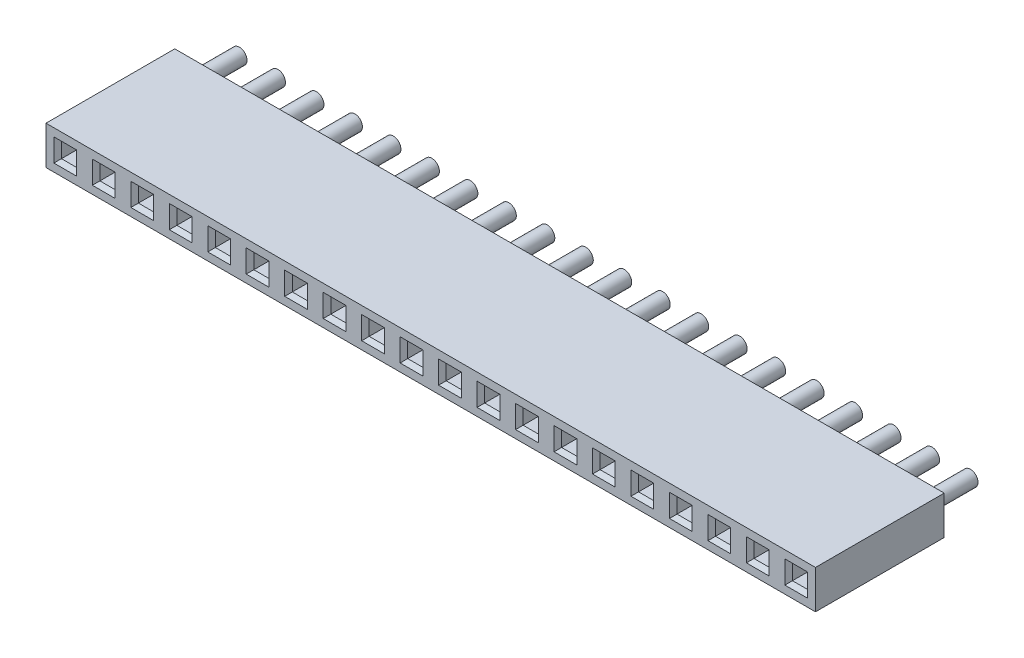
SolidWorks part; units mm, degrees
ref_plane "Front Plane" through (0, 0, 0) normal (0, 0, 1) x (1, 0, 0)
ref_plane "Top Plane" through (0, 0, 0) normal (0, 1, 0) x (1, 0, 0)
ref_plane "Right Plane" through (0, 0, 0) normal (1, 0, 0) x (0, 0, -1)
sketch "Sketch1" plane through (0, 0, 0) normal (0, 0, 1) x (1, 0, 0)
  line L1 (0, 0) -> (2.54, 0)
  line L2 (0, 0) -> (0, 2.54)
  line L3 (0, 2.54) -> (2.54, 2.54)
  line L4 (2.54, 0) -> (2.54, 2.54)
  dimension "D1" = 2.54
  dimension "D2" = 2.54
extrude "Boss-Extrude1" add sketch "Sketch1" along normal blind 8.5
sketch "Sketch2" plane through (0, 0, 8.5) normal (0, 0, 1) x (1, 0, 0)
  line L0 (0, 0) -> (2.54, 0) construction
  line L1 (0.77, 0.77) -> (1.77, 0.77)
  line L2 (0.77, 0.77) -> (0.77, 1.77)
  line L3 (0.77, 1.77) -> (1.77, 1.77)
  line L4 (1.77, 0.77) -> (1.77, 1.77)
  line L5 (0, 2.54) -> (0, 0) construction
  dimension "D1" = 1
  dimension "D2" = 1
  dimension "D3" = 0.77
  dimension "D4" = 0.77
extrude "Cut-Extrude1" cut sketch "Sketch2" against normal blind 8
chamfer "Chamfer1" distance 0.25 angle 45 4 edges at (1.27, 0.77, 8.5) (1.77, 1.27, 8.5) (0.77, 1.27, 8.5) (1.27, 1.77, 8.5)
sketch "Sketch3" plane through (0, 0, 0) normal (0, 0, -1) x (-1, 0, 0)
  line L0 (0, 0) -> (-2.54, 0) construction
  line L1 (0, 2.54) -> (0, 0) construction
  circle A0 centre (-1.27, 1.27) radius 0.5
  dimension "D1" = 1
  dimension "D2" = 1.27
  dimension "D3" = 1.27
extrude "Boss-Extrude2" add sketch "Sketch3" along normal blind 3
pattern_linear "LPattern3" count 20 spacing 2.54 along (1, 0, 0) of "Boss-Extrude1", "Boss-Extrude2", "Chamfer1", "Cut-Extrude1"
